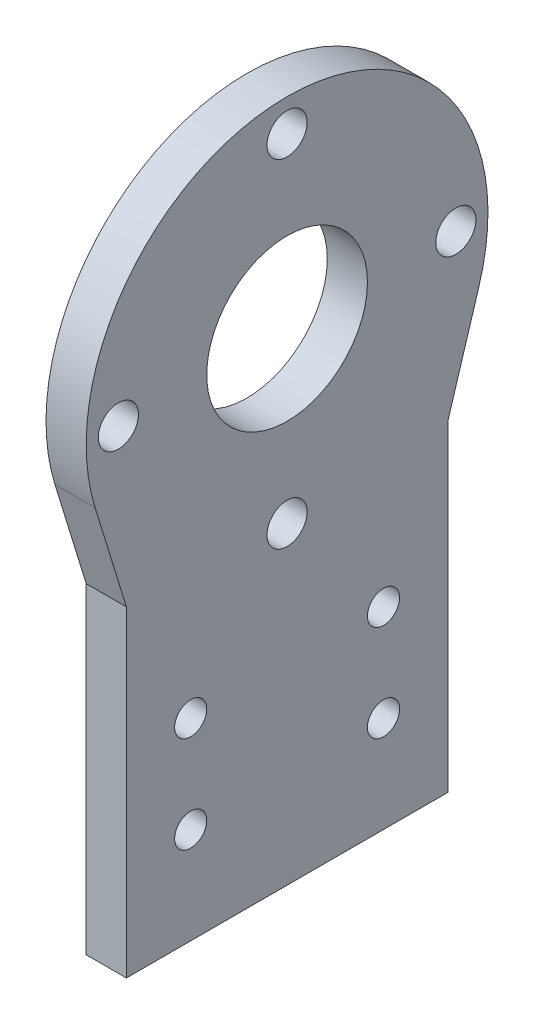
SolidWorks part; units mm, degrees
ref_plane "Alzado" through (0, 0, 0) normal (0, 0, 1) x (1, 0, 0)
ref_plane "Planta" through (0, 0, 0) normal (0, 1, 0) x (1, 0, 0)
ref_plane "Vista lateral" through (0, 0, 0) normal (1, 0, 0) x (0, 0, -1)
sketch "Croquis1" plane through (0, 0, 0) normal (1, 0, 0) x (0, 0, -1)
  line L0 (0, 0) -> (0, 40)
  line L1 (0, 40) -> (40, 40)
  line L2 (40, 40) -> (40, 0)
  line L3 (20, 40) -> (20, 60) construction
  line L4 (0, 0) -> (40, 0)
  line L5 (8, 24) -> (8, 12) construction
  line L6 (0, 40) -> (-3.893, 52.643)
  line L7 (40, 40) -> (43.893, 52.643)
  line L8 (8, 24) -> (32, 24) construction
  line L9 (8, 12) -> (32, 12) construction
  line L10 (32, 12) -> (32, 24) construction
  circle A0 centre (20, 60) radius 25
  circle A1 centre (20, 60) radius 10
  circle A2 centre (8, 24) radius 2
  circle A3 centre (8, 12) radius 2
  circle A4 centre (32, 12) radius 2
  circle A5 centre (32, 24) radius 2
  circle A6 centre (20, 60) radius 21 construction
  circle A7 centre (20, 81) radius 2.5
  circle A8 centre (41, 60) radius 2.5
  circle A9 centre (20, 39) radius 2.5
  circle A10 centre (-1, 60) radius 2.5
  point P31 (20, 60)
  dimension "D2" = 50
  dimension "D4" = 20
  dimension "D7" = 4
  dimension "D12" = 42
  dimension "D13" = 5
  dimension "D1" = 40
  dimension "D3" = 20
  dimension "D5" = 90
  dimension "D6" = 90
  dimension "D8" = 12
  dimension "D9" = 12
  dimension "D10" = 8
  dimension "D11" = 40
  dimension "D14" = 4
extrude "Saliente-Extruir1" add sketch "Croquis1" along normal blind 5 contours A0 L1 A1 | A0 L1 L0 L4 L2 A4 A3 A2 A5 | L1 A0 | A0 L6 L1 | A0 L1 L7
